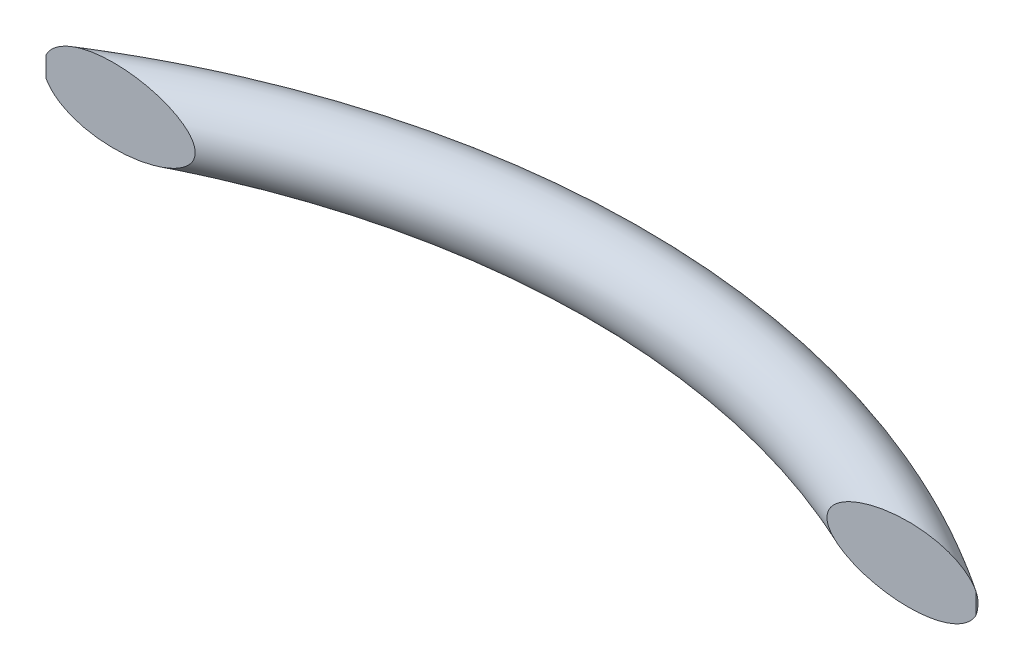
SolidWorks part; units mm, degrees
ref_plane "Front Plane" through (0, 0, 0) normal (0, 0, 1) x (1, 0, 0)
ref_plane "Top Plane" through (0, 0, 0) normal (0, 1, 0) x (1, 0, 0)
ref_plane "Right Plane" through (0, 0, 0) normal (1, 0, 0) x (0, 0, -1)
sketch "Sketch1" plane through (0, 0, 0) normal (0, 1, 0) x (1, 0, 0)
  line L0 (0, 0) -> (-304.8, 0) construction
  arc A0 (-304.8, 0) -> (0, 0) centre (-152.4, -227.8289) cw
  dimension "D1" = 304.8
ref_plane "Plane1" through (0, 0, 0) normal (0.8312, 0, 0.556) x (0.556, 0, -0.8312)
sketch "Sketch2" plane through (0, 0, 0) normal (0.8312, 0, 0.556) x (0.556, 0, -0.8312)
  circle A0 centre (0, 0) radius 12.7
  dimension "D1" = 25.4
sweep "Sweep1" add profiles "Sketch2" path "Sketch1"
sketch "Sketch3" plane through (0, 0, 0) normal (0, 0, 1) x (1, 0, 0)
  line L1 (-379.7255, 119.2139) -> (52.9389, 119.2139)
  line L2 (-379.7255, 119.2139) -> (-379.7255, -119.2139)
  line L3 (-379.7255, -119.2139) -> (52.9389, -119.2139)
  line L4 (52.9389, 119.2139) -> (52.9389, -119.2139)
  line L5 (-379.7255, 119.2139) -> (52.9389, -119.2139) construction
  line L6 (-379.7255, -119.2139) -> (52.9389, 119.2139) construction
  point P0 (-163.3933, 0)
extrude "Cut-Extrude2" cut sketch "Sketch3" against normal blind 10.16 and the other way blind 59.182
